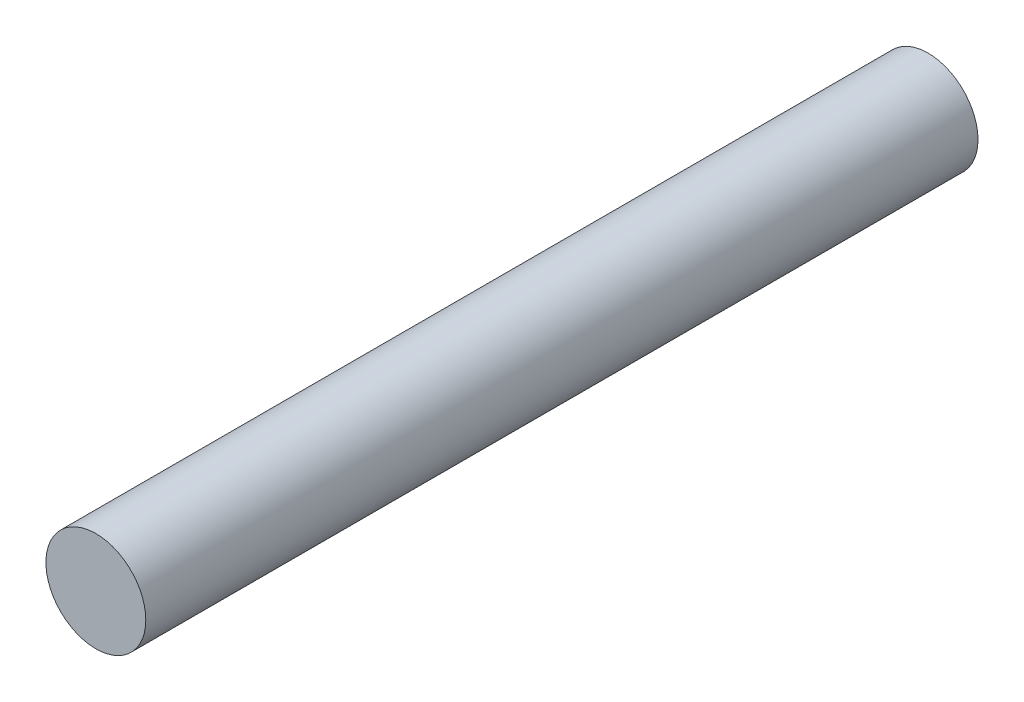
SolidWorks part; units mm, degrees
material "Plain Carbon Steel"
ref_plane "Front Plane" through (0, 0, 0) normal (0, 0, 1) x (1, 0, 0)
ref_plane "Top Plane" through (0, 0, 0) normal (0, 1, 0) x (1, 0, 0)
ref_plane "Right Plane" through (0, 0, 0) normal (1, 0, 0) x (0, 0, -1)
sketch "Sketch1" plane through (0, 0, 0) normal (0, 0, 1) x (1, 0, 0)
  circle A0 centre (0, 0) radius 1.5
  dimension "D1" = 3
extrude "Boss-Extrude1" add sketch "Sketch1" along normal blind 25
